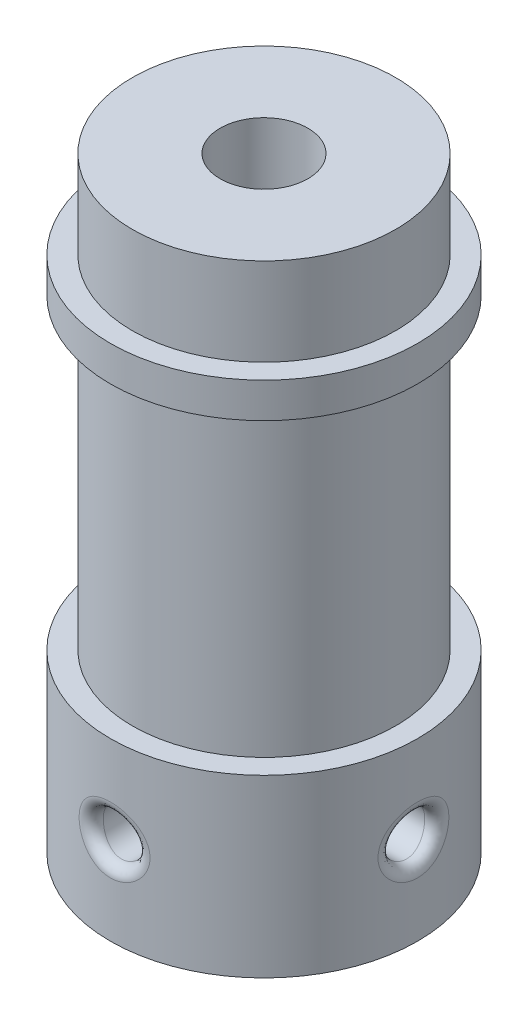
SolidWorks part; units mm, degrees
ref_plane "Front Plane" through (0, 0, 0) normal (0, 0, 1) x (1, 0, 0)
ref_plane "Top Plane" through (0, 0, 0) normal (0, 1, 0) x (1, 0, 0)
ref_plane "Right Plane" through (0, 0, 0) normal (1, 0, 0) x (0, 0, -1)
sketch "Sketch1" plane through (0, 0, 0) normal (0, 1, 0) x (1, 0, 0)
  line L0 (0, 0) -> (-13523.7469, 0) construction
  line L1 (0, 0) -> (0, 13523.7469) construction
  line L2 (7, 0) -> (44203.7332, -23380.5212) construction
  circle A0 centre (0, 0) radius 7
  dimension "D1" = 14
extrude "Boss-Extrude1" add sketch "Sketch1" along normal blind 8
sketch "Sketch2" plane through (0, 8, 0) normal (0, 1, 0) x (1, 0, 0)
  circle A0 centre (0, 0) radius 6
  dimension "D1" = 12
extrude "Boss-Extrude2" add sketch "Sketch2" along normal blind 14
sketch "Sketch3" plane through (0, 22, 0) normal (0, 1, 0) x (1, 0, 0)
  circle A0 centre (0, 0) radius 7
  dimension "D1" = 14
extrude "Boss-Extrude3" add sketch "Sketch3" along normal blind 1.6
sketch "Sketch4" plane through (0, 23.6, 0) normal (0, 1, 0) x (1, 0, 0)
  circle A0 centre (0, 0) radius 6
  dimension "D1" = 12
extrude "Boss-Extrude4" add sketch "Sketch4" along normal blind 4
sketch "Sketch5" plane through (0, 27.6, 0) normal (0, 1, 0) x (1, 0, 0)
  circle A0 centre (0, 0) radius 2
  dimension "D1" = 4
extrude "Cut-Extrude1" cut sketch "Sketch5" against normal through all
sketch "Sketch6" plane through (0, 0, 0) normal (0, -1, 0) x (1, 0, 0)
  circle A0 centre (0, 0) radius 3
  dimension "D1" = 6
extrude "Cut-Extrude2" cut sketch "Sketch6" against normal blind 20
sketch "Sketch7" plane through (0, 0, 0) normal (0, -1, 0) x (1, 0, 0)
  line L0 (0, 3) -> (0, 7) construction
  circle A0 centre (0, 0) radius 3 construction
  circle A1 centre (0, 0) radius 7 construction
ref_plane "Plane1" through (0, 0, 7) normal (0, 0, 1) x (1, 0, 0)
sketch "Sketch8" plane through (0, 0, 7) normal (0, 0, 1) x (1, 0, 0)
  line L0 (0, 0) -> (0, 50000) construction
  circle A0 centre (0, 4) radius 1
  dimension "D1" = 2
extrude "Cut-Extrude3" cut sketch "Sketch8" against normal up to next
pattern_circular "CirPattern1" count 2 every 90 about axis through (0, 0, 0) along (0, 1, 0) of "Cut-Extrude3"
fillet "Fillet1" radius 0.5 2 edges at (6.9317, 3.7814, 0.9758) (-0.9758, 3.7814, 6.9317)
